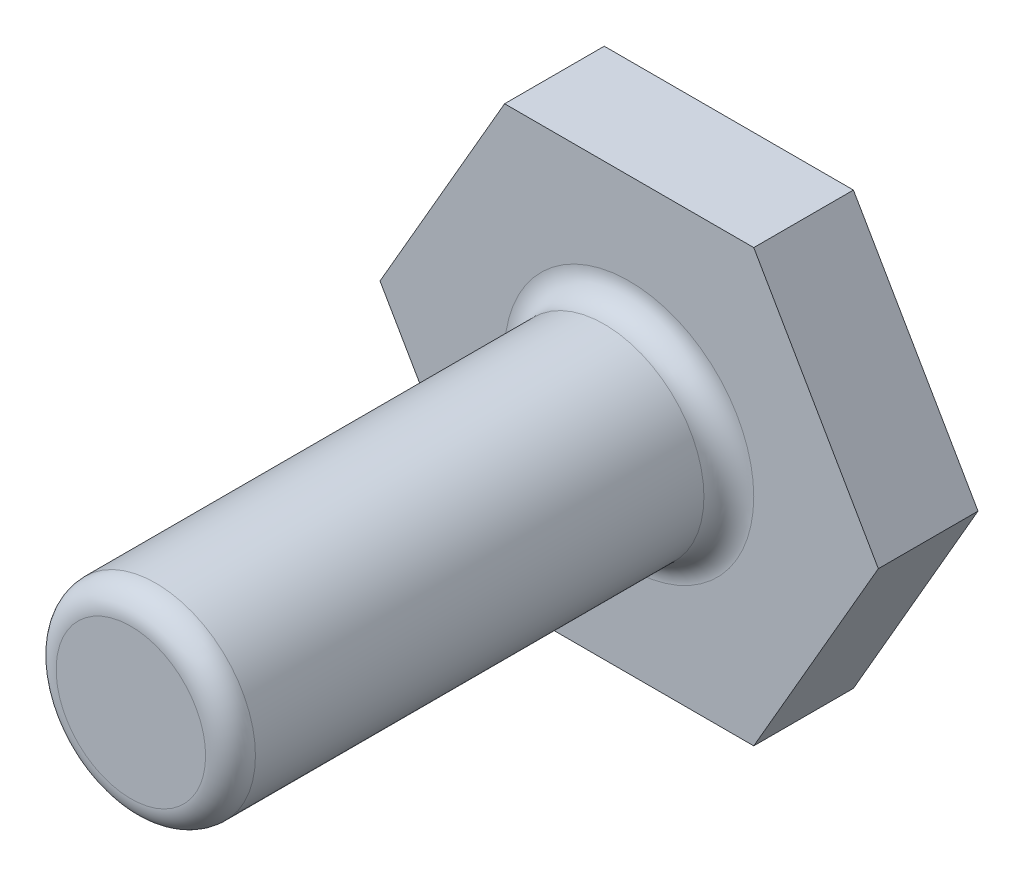
SolidWorks part; units mm, degrees
ref_plane "Front" through (0, 0, 0) normal (0, 0, 1) x (1, 0, 0)
ref_plane "Top" through (0, 0, 0) normal (0, 1, 0) x (1, 0, 0)
ref_plane "Right" through (0, 0, 0) normal (1, 0, 0) x (0, 0, -1)
sketch "Sketch2" plane through (0, 0, 0) normal (0, 0, 1) x (1, 0, 0)
  line L1 (-10, 0) -> (-5, -8.6603)
  line L2 (-5, -8.6603) -> (5, -8.6603)
  line L3 (5, -8.6603) -> (10, 0)
  line L4 (10, 0) -> (5, 8.6603)
  line L5 (5, 8.6603) -> (-5, 8.6603)
  line L6 (-5, 8.6603) -> (-10, 0)
  circle A0 centre (0, 0) radius 8.6603 construction
  dimension "D1" = 10
extrude "Boss-Extrude1" add sketch "Sketch2" along normal blind 4
sketch "Sketch3" plane through (0, 0, 4) normal (0, 0, 1) x (1, 0, 0)
  circle A0 centre (0, 0) radius 4
extrude "Boss-Extrude2" add sketch "Sketch3" along normal blind 20
fillet "Fillet2" radius 1 2 edges at (4, 0, 24) (4, 0, 4)
equation "\"4.oo\"=10"
